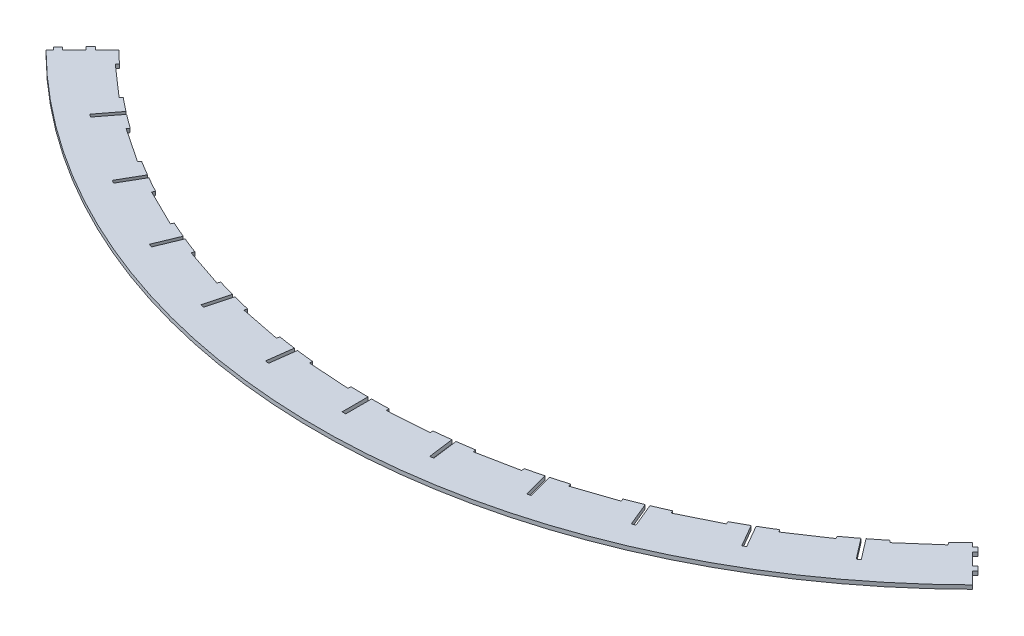
SolidWorks part; units mm, degrees
ref_plane "前视基准面" through (0, 0, 0) normal (0, 0, 1) x (1, 0, 0)
ref_plane "上视基准面" through (0, 0, 0) normal (0, 1, 0) x (1, 0, 0)
ref_plane "右视基准面" through (0, 0, 0) normal (1, 0, 0) x (0, 0, -1)
sketch "草图1" plane through (0, 0, 0) normal (0, 1, 0) x (1, 0, 0)
  line L0 (0, 0) -> (-180.0435, -180.0435) construction
  line L1 (0, 0) -> (180.0435, -180.0435) construction
  line L2 (0, 74.2982) -> (0, -109.8902) construction
  line L3 (-165.9014, -165.9014) -> (-180.0435, -180.0435)
  line L4 (180.0435, -180.0435) -> (165.9014, -165.9014)
  arc A0 (-180.0435, -180.0435) -> (180.0435, -180.0435) centre (0, 0) ccw
  arc A1 (-165.9014, -165.9014) -> (165.9014, -165.9014) centre (0, 0) ccw
  dimension "D1" = 90
  dimension "D3" = 254.62
  dimension "D4" = 20
  dimension "D2" = 45
extrude "凸台-拉伸1" add sketch "草图1" along normal blind 1.5
sketch "草图4" plane through (0, 1.5, 0) normal (0, 1, 0) x (1, 0, 0)
  line L0 (-180.0435, -180.0435) -> (0, 0) construction
  line L1 (0, 0) -> (-155.0028, -202.0036) construction
  line L2 (0, 0) -> (-167.8826, -191.4335) construction
  line L3 (-161.3698, -171.8737) -> (-160.0511, -170.37)
  line L4 (-161.3698, -171.8737) -> (-149.3403, -182.4233)
  line L5 (-160.0511, -170.37) -> (-148.0217, -180.9196)
  line L6 (-149.3403, -182.4233) -> (-148.0217, -180.9196)
  line L7 (-161.3698, -171.8737) -> (-148.0217, -180.9196) construction
  line L8 (-160.0511, -170.37) -> (-149.3403, -182.4233) construction
  arc A0 (-180.0435, -180.0435) -> (180.0435, -180.0435) centre (0, 0) ccw construction
  arc A1 (-165.9014, -165.9014) -> (165.9014, -165.9014) centre (0, 0) ccw construction
  point P11 (-154.6957, -176.3967)
  dimension "D1" = 7.5
  dimension "D2" = 3.75
  dimension "D3" = 16
  dimension "D4" = 2
extrude "切除-拉伸2" cut sketch "草图4" against normal up to next (1.5 mm away)
pattern_circular "阵列(圆周)1" count 12 every 7.5 about axis through (0, 0, 0) along (0, 1, 0) of "切除-拉伸2"
sketch "草图5" plane through (0, 1.5, 0) normal (0, 1, 0) x (1, 0, 0)
  line L0 (-180.0435, -180.0435) -> (0, 0) construction
  line L1 (0, 0) -> (-155.0028, -202.0036) construction
  line L2 (-149.4706, -193.644) -> (-137.2953, -177.7769)
  line L3 (-149.4706, -193.644) -> (-148.3599, -194.4962)
  line L4 (-137.2953, -177.7769) -> (-136.1846, -178.6292)
  line L5 (-148.3599, -194.4962) -> (-136.1846, -178.6292)
  line L6 (-149.4706, -193.644) -> (-136.1846, -178.6292) construction
  line L7 (-137.2953, -177.7769) -> (-148.3599, -194.4962) construction
  arc A0 (-180.0435, -180.0435) -> (180.0435, -180.0435) centre (0, 0) ccw construction
  arc A1 (-148.591, -181.5688) -> (-136.9238, -190.5214) centre (0, 0) ccw construction
  point P9 (-142.8276, -186.1366)
  point P10 (-148.9152, -194.0701)
  dimension "D1" = 7.5
  dimension "D2" = 1.4
  dimension "D3" = 10
extrude "切除-拉伸3" cut sketch "草图5" against normal up to next (1.5 mm away)
pattern_circular "阵列(圆周)2" count 11 every 7.5 about axis through (0, 0, 0) along (0, 1, 0) of "切除-拉伸3"
sketch "草图2" plane through (0, 1.5, 0) normal (0, 1, 0) x (1, 0, 0)
  line L0 (0, 0) -> (-180.0435, -180.0435) construction
  line L1 (-186.1091, -185.0485) -> (-149.8643, -148.8037)
  line L2 (-186.1091, -185.0485) -> (-185.0485, -186.1091)
  line L3 (-149.8643, -148.8037) -> (-148.8037, -149.8643)
  line L4 (-185.0485, -186.1091) -> (-148.8037, -149.8643)
  line L5 (-186.1091, -185.0485) -> (-148.8037, -149.8643) construction
  line L6 (-149.8643, -148.8037) -> (-185.0485, -186.1091) construction
  line L7 (0, 0) -> (180.0435, -180.0435) construction
  line L8 (182.0435, -183.1042) -> (140.8203, -141.8809)
  line L9 (182.0435, -183.1042) -> (183.1042, -182.0435)
  line L10 (140.8203, -141.8809) -> (141.8809, -140.8203)
  line L11 (183.1042, -182.0435) -> (141.8809, -140.8203)
  line L12 (182.0435, -183.1042) -> (141.8809, -140.8203) construction
  line L13 (140.8203, -141.8809) -> (183.1042, -182.0435) construction
  point P5 (-167.4564, -167.4564)
  point P7 (161.9622, -161.9622)
  dimension "D1" = 1.5
  dimension "D2" = 1.5
extrude "切除-拉伸1" cut sketch "草图2" against normal up to next
sketch "草图3" plane through (0, 1.5, 0) normal (0, 1, 0) x (1, 0, 0)
  line L0 (173.1484, -174.2091) -> (174.9162, -175.9768)
  line L1 (173.1484, -174.2091) -> (174.2091, -173.1484)
  line L2 (174.9162, -175.9768) -> (175.9768, -174.9162)
  line L3 (174.2091, -173.1484) -> (175.9768, -174.9162)
  line L4 (165.3702, -166.4309) -> (179.5124, -180.5731) construction
  line L5 (168.5522, -169.6129) -> (166.7844, -167.8451)
  line L6 (168.5522, -169.6129) -> (169.6129, -168.5522)
  line L7 (166.7844, -167.8451) -> (167.8451, -166.7844)
  line L8 (169.6129, -168.5522) -> (167.8451, -166.7844)
  line L9 (-178.0982, -179.1589) -> (-176.3304, -177.3911)
  line L10 (-178.0982, -179.1589) -> (-179.1589, -178.0982)
  line L11 (-176.3304, -177.3911) -> (-177.3911, -176.3304)
  line L12 (-179.1589, -178.0982) -> (-177.3911, -176.3304)
  line L13 (-179.5124, -180.5731) -> (-165.3702, -166.4309) construction
  line L14 (-171.7342, -172.7949) -> (-169.9665, -171.0271)
  line L15 (-171.7342, -172.7949) -> (-172.8303, -171.6989)
  line L16 (-169.9665, -171.0271) -> (-171.0625, -169.9311)
  line L17 (-172.8303, -171.6989) -> (-171.0625, -169.9311)
  point P4 (169.0825, -169.0825)
  dimension "D1" = 2.5
  dimension "D2" = 2.5
  dimension "D3" = 2
  dimension "D4" = 9
  dimension "D5" = 1.5
  dimension "D6" = 1.5
  dimension "D7" = 2
  dimension "D8" = 1.5
  dimension "D9" = 9
  dimension "D10" = 2.5
  dimension "D11" = 2.5
  dimension "D12" = 1.55
extrude "凸台-拉伸2" add sketch "草图3" against normal blind 1.5
